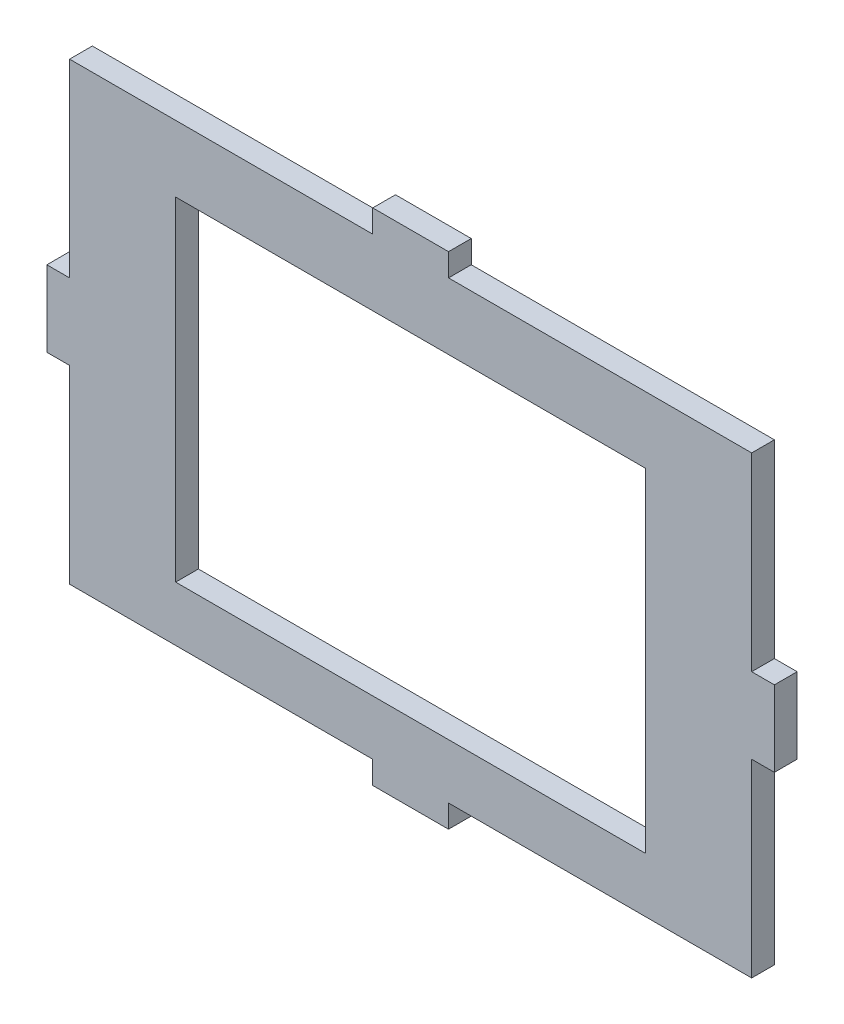
SolidWorks part; units mm, degrees
ref_plane "Alzado" through (0, 0, 0) normal (0, 0, 1) x (1, 0, 0)
ref_plane "Planta" through (0, 0, 0) normal (0, 1, 0) x (1, 0, 0)
ref_plane "Vista lateral" through (0, 0, 0) normal (1, 0, 0) x (0, 0, -1)
sketch "Croquis1" plane through (0, 0, 0) normal (0, 0, 1) x (1, 0, 0)
  line L0 (0, 0) -> (89.987, 1.5276) construction
  line L1 (44.9935, 0.7638) -> (44.4843, 30.7595) construction
  line L2 (44.9935, 0.7638) -> (44.9935, -29.2362) construction
  line L4 (0, 30.7595) -> (89.987, 30.7595)
  line L5 (0, 30.7595) -> (0, -29.2362)
  line L6 (0, -29.2362) -> (89.987, -29.2362)
  line L7 (89.987, 30.7595) -> (89.987, -29.2362)
extrude "Saliente-Extruir1" add sketch "Croquis1" along normal blind 3
sketch "Croquis2" plane through (0, 0, 3) normal (0, 0, 1) x (1, 0, 0)
  line L0 (44.9935, 0) -> (44.9935, 22) construction
  line L1 (44.9935, 0) -> (44.9935, -22) construction
  line L2 (44.9935, 0) -> (75.9935, 0) construction
  line L3 (44.9935, 0) -> (13.9935, 0) construction
  line L5 (13.9935, 22) -> (75.9935, 22)
  line L6 (13.9935, 22) -> (13.9935, -22)
  line L7 (13.9935, -22) -> (75.9935, -22)
  line L8 (75.9935, 22) -> (75.9935, -22)
  point P0 (44.9935, 0)
extrude "Cortar-Extruir1" cut sketch "Croquis2" against normal blind 3
sketch "Croquis3" plane through (0, 30.7595, 0) normal (0, 1, 0) x (1, 0, 0)
  line L0 (44.9935, 0) -> (44.9935, -3) construction
  line L1 (89.987, 0) -> (0, 0) construction
  line L2 (89.987, -3) -> (0, -3) construction
  line L4 (44.9935, 0) -> (49.9935, 0)
  line L5 (44.9935, 0) -> (44.9935, -3)
  line L6 (44.9935, -3) -> (49.9935, -3)
  line L7 (49.9935, 0) -> (49.9935, -3)
  line L8 (44.9935, 0) -> (39.9935, 0)
  line L9 (44.9935, 0) -> (44.9935, -3)
  line L10 (44.9935, -3) -> (39.9935, -3)
  line L11 (39.9935, 0) -> (39.9935, -3)
  line L12 (39.9935, 0) -> (49.9935, 0)
  line L13 (39.9935, 0) -> (39.9935, -3)
  line L14 (39.9935, -3) -> (49.9935, -3)
  line L15 (49.9935, 0) -> (49.9935, -3)
  line M6 (89.987, 0) -> (0, 0)
  line M8 (0, -3) -> (89.987, -3)
extrude "Saliente-Extruir2" add sketch "Croquis3" along normal blind 3 contours L7 L5 M6 M8 | L11 L5 M6 M8
sketch "Croquis4" plane through (0, -29.2362, 0) normal (0, -1, 0) x (1, 0, 0)
  line L0 (44.9935, 3) -> (44.9935, 0) construction
  line L1 (0, 3) -> (89.987, 3) construction
  line L2 (0, 0) -> (89.987, 0) construction
  line L4 (44.9935, 0) -> (39.9935, 0)
  line L5 (44.9935, 0) -> (44.9935, 3)
  line L6 (44.9935, 3) -> (39.9935, 3)
  line L7 (39.9935, 0) -> (39.9935, 3)
  line L8 (44.9935, 0) -> (49.9935, 0)
  line L9 (44.9935, 0) -> (44.9935, 3)
  line L10 (44.9935, 3) -> (49.9935, 3)
  line L11 (49.9935, 0) -> (49.9935, 3)
  line M8 (0, 0) -> (89.987, 0)
  line M10 (89.987, 3) -> (0, 3)
extrude "Saliente-Extruir3" add sketch "Croquis4" along normal blind 3 contours L11 L5 M8 M10 | L7 L5 M8 M10
sketch "Croquis5" plane through (89.987, 0, 0) normal (1, 0, 0) x (0, 0, -1)
  line L0 (-3, 0.7617) -> (0, 0.7617) construction
  line L1 (-3, -29.2362) -> (-3, 30.7595) construction
  line L2 (0, -29.2362) -> (0, 30.7595) construction
  line L4 (-3, 0.7617) -> (0, 0.7617)
  line L5 (-3, 0.7617) -> (-3, 5.7617)
  line L6 (-3, 5.7617) -> (0, 5.7617)
  line L7 (0, 0.7617) -> (0, 5.7617)
  line L8 (-3, 0.7617) -> (0, 0.7617)
  line L9 (-3, 0.7617) -> (-3, -4.2383)
  line L10 (-3, -4.2383) -> (0, -4.2383)
  line L11 (0, 0.7617) -> (0, -4.2383)
  line M9 (0, -29.2362) -> (0, 30.7595)
  line M11 (-3, 30.7595) -> (-3, -29.2362)
extrude "Saliente-Extruir4" add sketch "Croquis5" along normal blind 3 contours L6 L4 M11 M9 | L10 L4 M11 M9
sketch "Croquis6" plane through (0, 0, 0) normal (-1, 0, 0) x (0, 0, 1)
  line L0 (3, 0.7617) -> (0, 0.7617) construction
  line L2 (3, 30.7595) -> (3, -29.2362) construction
  line L3 (0, 30.7595) -> (0, -29.2362) construction
  line L5 (3, 0.7617) -> (0, 0.7617)
  line L6 (3, 0.7617) -> (3, 5.7617)
  line L7 (3, 5.7617) -> (0, 5.7617)
  line L8 (0, 0.7617) -> (0, 5.7617)
  line L9 (3, 0.7617) -> (0, 0.7617)
  line L10 (3, 0.7617) -> (3, -4.2383)
  line L11 (3, -4.2383) -> (0, -4.2383)
  line L12 (0, 0.7617) -> (0, -4.2383)
  line M9 (0, 30.7595) -> (0, -29.2362)
  line M11 (3, -29.2362) -> (3, 30.7595)
extrude "Saliente-Extruir5" add sketch "Croquis6" along normal blind 3 contours L7 L5 M11 M9 | L11 L5 M11 M9
